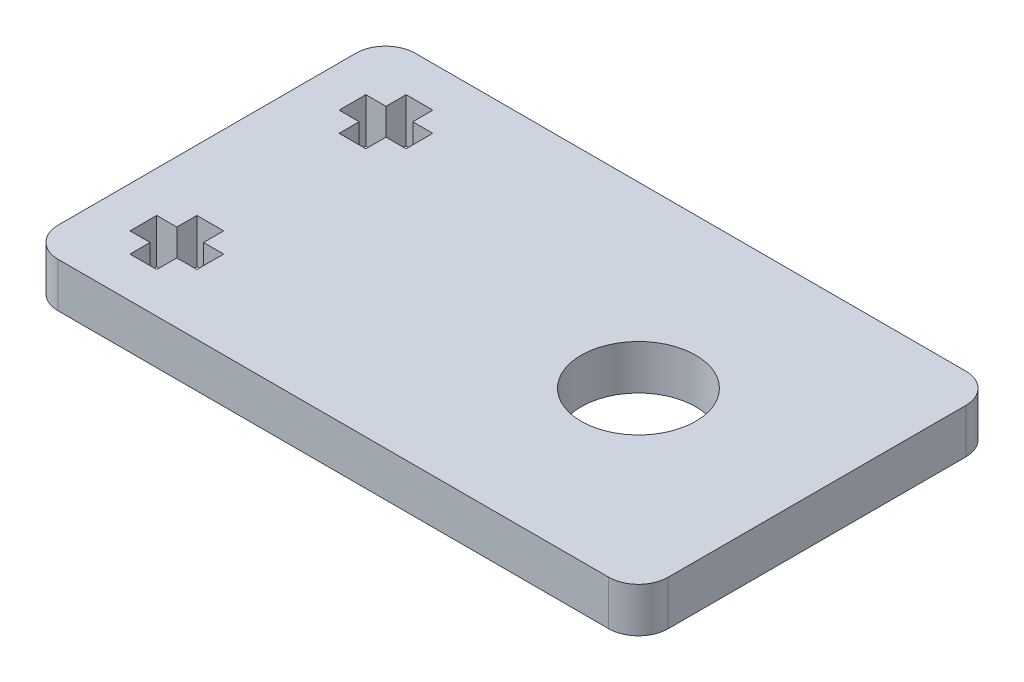
SolidWorks part; units mm, degrees
ref_plane "Front Plane" through (0, 0, 0) normal (0, 0, 1) x (1, 0, 0)
ref_plane "Top Plane" through (0, 0, 0) normal (0, 1, 0) x (1, 0, 0)
ref_plane "Right Plane" through (0, 0, 0) normal (1, 0, 0) x (0, 0, -1)
sketch "Sketch1" plane through (0, 0, 0) normal (0, 1, 0) x (1, 0, 0)
  line L0 (-21.75, -6.1294) -> (-23.1, -6.1294) construction
  line L1 (-29, -12) -> (29, -12)
  line L2 (-29, -12) -> (-29, 12)
  line L3 (-29, 12) -> (29, 12)
  line L4 (29, -12) -> (29, -6)
  line L5 (-29, -12) -> (29, 12) construction
  line L6 (-29, 12) -> (29, -12) construction
  line L7 (-23.1, 6.1294) -> (-21.75, 6.1294) construction
  line L8 (-21.75, -6.1294) -> (-23.1, -6.1294)
  line L9 (-23.1, 6.1294) -> (-21.75, 6.1294)
  line L10 (-21.75, -7.9294) -> (-21.75, -6.1294) construction
  line L11 (-23.1, -7.9294) -> (-21.75, -7.9294) construction
  line L12 (-24.9, -4.7794) -> (-24.9, -6.1294) construction
  line L13 (-23.1, -4.7794) -> (-24.9, -4.7794) construction
  line L14 (-23.1, -6.1294) -> (-23.1, -4.7794) construction
  line L15 (-24.9, -6.1294) -> (-26.25, -6.1294) construction
  line L16 (-26.25, -6.1294) -> (-26.25, -7.9294) construction
  line L17 (-26.25, -7.9294) -> (-24.9, -7.9294) construction
  line L18 (-24.9, -7.9294) -> (-24.9, -9.2794) construction
  line L19 (-23.1, -9.2794) -> (-23.1, -7.9294) construction
  line L20 (-24.9, -9.2794) -> (-23.1, -9.2794) construction
  line L21 (-24.9, -9.2794) -> (-23.1, -9.2794)
  line L22 (-23.1, -9.2794) -> (-23.1, -7.9294)
  line L23 (-24.9, -7.9294) -> (-24.9, -9.2794)
  line L24 (-26.25, -7.9294) -> (-24.9, -7.9294)
  line L25 (-26.25, -6.1294) -> (-26.25, -7.9294)
  line L26 (-24.9, -6.1294) -> (-26.25, -6.1294)
  line L27 (-23.1, -6.1294) -> (-23.1, -4.7794)
  line L28 (-23.1, -4.7794) -> (-24.9, -4.7794)
  line L29 (-24.9, -4.7794) -> (-24.9, -6.1294)
  line L30 (-23.1, -7.9294) -> (-21.75, -7.9294)
  line L31 (-21.75, -7.9294) -> (-21.75, -6.1294)
  line L32 (-23.1, 4.7794) -> (-23.1, 6.1294) construction
  line L33 (-23.1, 4.7794) -> (-23.1, 6.1294)
  line L34 (-21.75, 6.1294) -> (-21.75, 7.9294) construction
  line L35 (-21.75, 7.9294) -> (-23.1, 7.9294) construction
  line L36 (-23.1, 7.9294) -> (-23.1, 9.2794) construction
  line L37 (-23.1, 9.2794) -> (-24.9, 9.2794) construction
  line L38 (-24.9, 9.2794) -> (-24.9, 7.9294) construction
  line L39 (-26.25, 6.1294) -> (-24.9, 6.1294) construction
  line L40 (-24.9, 7.9294) -> (-26.25, 7.9294) construction
  line L41 (-26.25, 7.9294) -> (-26.25, 6.1294) construction
  line L42 (-24.9, 6.1294) -> (-24.9, 4.7794) construction
  line L43 (-24.9, 4.7794) -> (-23.1, 4.7794) construction
  line L44 (-21.75, 6.1294) -> (-21.75, 7.9294)
  line L45 (-21.75, 7.9294) -> (-23.1, 7.9294)
  line L46 (-23.1, 7.9294) -> (-23.1, 9.2794)
  line L47 (-23.1, 9.2794) -> (-24.9, 9.2794)
  line L48 (-24.9, 9.2794) -> (-24.9, 7.9294)
  line L49 (-26.25, 6.1294) -> (-24.9, 6.1294)
  line L50 (-24.9, 7.9294) -> (-26.25, 7.9294)
  line L51 (-26.25, 7.9294) -> (-26.25, 6.1294)
  line L52 (-24.9, 6.1294) -> (-24.9, 4.7794)
  line L53 (-24.9, 4.7794) -> (-23.1, 4.7794)
  line L61 (21.6, 6) -> (29, 6)
  line L62 (29, -6) -> (21.6, -6)
  line L63 (21.6, -6) -> (21.6, -0.5) construction
  line L64 (21.6, -6) -> (26.6, -6) construction
  line L68 (29, 6) -> (29, 12)
  line L69 (21.6, -6) -> (21.6, 6)
  circle A0 centre (0, 0) radius 3.85
  circle A1 centre (23.8, 9) radius 2.25 construction
  circle A2 centre (23.8, 9) radius 2.25
  circle A3 centre (23.8, -9) radius 2.25 construction
  circle A4 centre (23.8, -9) radius 2.25
  point P0 (0, 0)
  dimension "D1" = 7.7
  dimension "D2" = 58
  dimension "D3" = 24
extrude "Boss-Extrude1" add sketch "Sketch1" along normal blind 3
fillet "Fillet1" radius 2 8 edges at (29, 1.5, 12) (29, 1.5, 6) (21.6, 1.5, 6) (21.6, 1.5, -6) (29, 1.5, -6) (29, 1.5, -12) (-29, 1.5, 12) (-29, 1.5, -12)
sketch "Sketch2" plane through (0, 3, 0) normal (0, 1, 0) x (1, 0, 0)
  line L1 (47.3725, -21.6599) -> (12, -21.6599)
  line L2 (47.3725, -21.6599) -> (47.3725, 21.0627)
  line L3 (47.3725, 21.0627) -> (12, 21.0627)
  line L4 (12, -21.6599) -> (12, 21.0627)
  line L5 (47.3725, -21.6599) -> (12, 21.0627) construction
  line L6 (47.3725, 21.0627) -> (12, -21.6599) construction
  point P0 (29.6863, -0.2986)
  dimension "D1" = 12
extrude "Cut-Extrude1" cut sketch "Sketch2" against normal blind 10
fillet "Fillet2" radius 2 2 edges at (12, 1.5, 12) (12, 1.5, -12)
sketch "Sketch3" plane through (0, 3, 0) normal (0, 1, 0) x (1, 0, 0)
  line L4 (-27, -12) -> (10, -12)
  line L5 (12, -10) -> (12, 10)
  line L6 (10, 12) -> (-27, 12)
  line L7 (-29, 10) -> (-29, -10)
  line L8 (-27, -12) -> (10, -12)
  line L9 (12, -10) -> (12, 10)
  line L10 (10, 12) -> (-27, 12)
  line L11 (-29, 10) -> (-29, -10)
  line L12 (-23.1, 4.7794) -> (-23.1, 6.1294)
  line L13 (-24.9, 4.7794) -> (-23.1, 4.7794)
  line L14 (-24.9, 6.1294) -> (-24.9, 4.7794)
  line L15 (-26.25, 6.1294) -> (-24.9, 6.1294)
  line L16 (-26.25, 7.9294) -> (-26.25, 6.1294)
  line L17 (-24.9, 7.9294) -> (-26.25, 7.9294)
  line L18 (-24.9, 9.2794) -> (-24.9, 7.9294)
  line L19 (-23.1, 9.2794) -> (-24.9, 9.2794)
  line L20 (-23.1, 7.9294) -> (-23.1, 9.2794)
  line L21 (-21.75, 7.9294) -> (-23.1, 7.9294)
  line L22 (-21.75, 6.1294) -> (-21.75, 7.9294)
  line L23 (-23.1, 6.1294) -> (-21.75, 6.1294)
  line L24 (-23.1, 4.7794) -> (-23.1, 6.1294)
  line L25 (-24.9, 4.7794) -> (-23.1, 4.7794)
  line L26 (-24.9, 6.1294) -> (-24.9, 4.7794)
  line L27 (-26.25, 6.1294) -> (-24.9, 6.1294)
  line L28 (-26.25, 7.9294) -> (-26.25, 6.1294)
  line L29 (-24.9, 7.9294) -> (-26.25, 7.9294)
  line L30 (-24.9, 9.2794) -> (-24.9, 7.9294)
  line L31 (-23.1, 9.2794) -> (-24.9, 9.2794)
  line L32 (-23.1, 7.9294) -> (-23.1, 9.2794)
  line L33 (-21.75, 7.9294) -> (-23.1, 7.9294)
  line L34 (-21.75, 6.1294) -> (-21.75, 7.9294)
  line L35 (-23.1, 6.1294) -> (-21.75, 6.1294)
  line L36 (-21.75, -7.9294) -> (-21.75, -6.1294)
  line L37 (-23.1, -7.9294) -> (-21.75, -7.9294)
  line L38 (-23.1, -9.2794) -> (-23.1, -7.9294)
  line L39 (-24.9, -9.2794) -> (-23.1, -9.2794)
  line L40 (-24.9, -7.9294) -> (-24.9, -9.2794)
  line L41 (-26.25, -7.9294) -> (-24.9, -7.9294)
  line L42 (-26.25, -6.1294) -> (-26.25, -7.9294)
  line L43 (-24.9, -6.1294) -> (-26.25, -6.1294)
  line L44 (-24.9, -4.7794) -> (-24.9, -6.1294)
  line L45 (-23.1, -4.7794) -> (-24.9, -4.7794)
  line L46 (-23.1, -6.1294) -> (-23.1, -4.7794)
  line L47 (-21.75, -6.1294) -> (-23.1, -6.1294)
  line L48 (-21.75, -7.9294) -> (-21.75, -6.1294)
  line L49 (-23.1, -7.9294) -> (-21.75, -7.9294)
  line L50 (-23.1, -9.2794) -> (-23.1, -7.9294)
  line L51 (-24.9, -9.2794) -> (-23.1, -9.2794)
  line L52 (-24.9, -7.9294) -> (-24.9, -9.2794)
  line L53 (-26.25, -7.9294) -> (-24.9, -7.9294)
  line L54 (-26.25, -6.1294) -> (-26.25, -7.9294)
  line L55 (-24.9, -6.1294) -> (-26.25, -6.1294)
  line L56 (-24.9, -4.7794) -> (-24.9, -6.1294)
  line L57 (-23.1, -4.7794) -> (-24.9, -4.7794)
  line L58 (-23.1, -6.1294) -> (-23.1, -4.7794)
  line L59 (-21.75, -6.1294) -> (-23.1, -6.1294)
  circle A1 centre (0, 0) radius 3.85
  circle A2 centre (0, 0) radius 3.85
  arc A6 (10, -12) -> (12, -10) centre (10, -10) ccw
  arc A7 (12, 10) -> (10, 12) centre (10, 10) ccw
  arc A8 (-27, 12) -> (-29, 10) centre (-27, 10) ccw
  arc A9 (-29, -10) -> (-27, -12) centre (-27, -10) ccw
  arc A10 (10, -12) -> (12, -10) centre (10, -10) ccw
  arc A11 (12, 10) -> (10, 12) centre (10, 10) ccw
  arc A12 (-27, 12) -> (-29, 10) centre (-27, 10) ccw
  arc A13 (-29, -10) -> (-27, -12) centre (-27, -10) ccw
  dimension "D1" = 0
  dimension "D2" = 0
  dimension "D3" = 0
  dimension "D4" = 0
